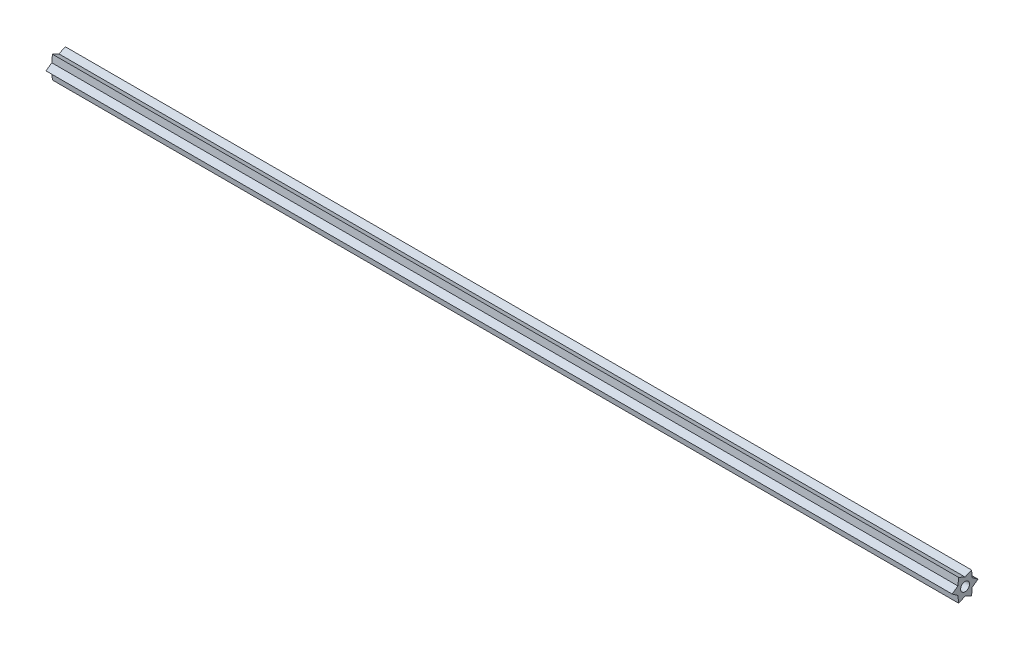
SolidWorks part; units mm, degrees
ref_plane "Front" through (0, 0, 0) normal (0, 0, 1) x (1, 0, 0)
ref_plane "Top" through (0, 0, 0) normal (0, 1, 0) x (1, 0, 0)
ref_plane "Right" through (0, 0, 0) normal (1, 0, 0) x (0, 0, -1)
sketch "Sketch1" plane through (0, 0, 0) normal (1, 0, 0) x (0, 0, -1)
  line L0 (-3.6662, 6.35) -> (0, 4.6991)
  line L1 (7.3323, 0) -> (3.6662, 6.35) construction
  line L2 (3.6662, 6.35) -> (-3.6662, 6.35) construction
  line L3 (-3.6662, 6.35) -> (-7.3323, 0) construction
  line L4 (-7.3323, 0) -> (-3.6662, -6.35) construction
  line L5 (-3.6662, -6.35) -> (3.6662, -6.35) construction
  line L6 (3.6662, -6.35) -> (7.3323, 0) construction
  line L7 (0, 4.6991) -> (3.6662, 6.35)
  line L8 (3.6662, 6.35) -> (4.0695, 2.3495)
  line L9 (4.0695, 2.3495) -> (7.3323, 0)
  line L10 (7.3323, 0) -> (4.0695, -2.3495)
  line L11 (4.0695, -2.3495) -> (3.6662, -6.35)
  line L12 (3.6662, -6.35) -> (0, -4.6991)
  line L13 (0, -4.6991) -> (-3.6662, -6.35)
  line L14 (-3.6662, -6.35) -> (-4.0695, -2.3495)
  line L15 (-4.0695, -2.3495) -> (-7.3323, 0)
  line L16 (-7.3323, 0) -> (-4.0695, 2.3495)
  line L17 (-4.0695, 2.3495) -> (-3.6662, 6.35)
  circle A0 centre (0, 0) radius 6.35 construction
  point P27 (0, 0)
  dimension "D1" = 6
extrude "Boss-Extrude1" add sketch "Sketch1" along normal blind 514.35
sketch "Sketch2" plane through (514.35, 0, 0) normal (1, 0, 0) x (0, 0, -1)
  circle A0 centre (0, 0) radius 2.54
  dimension "D1" = 5.08
extrude "Cut-Extrude1" cut sketch "Sketch2" against normal up to next
